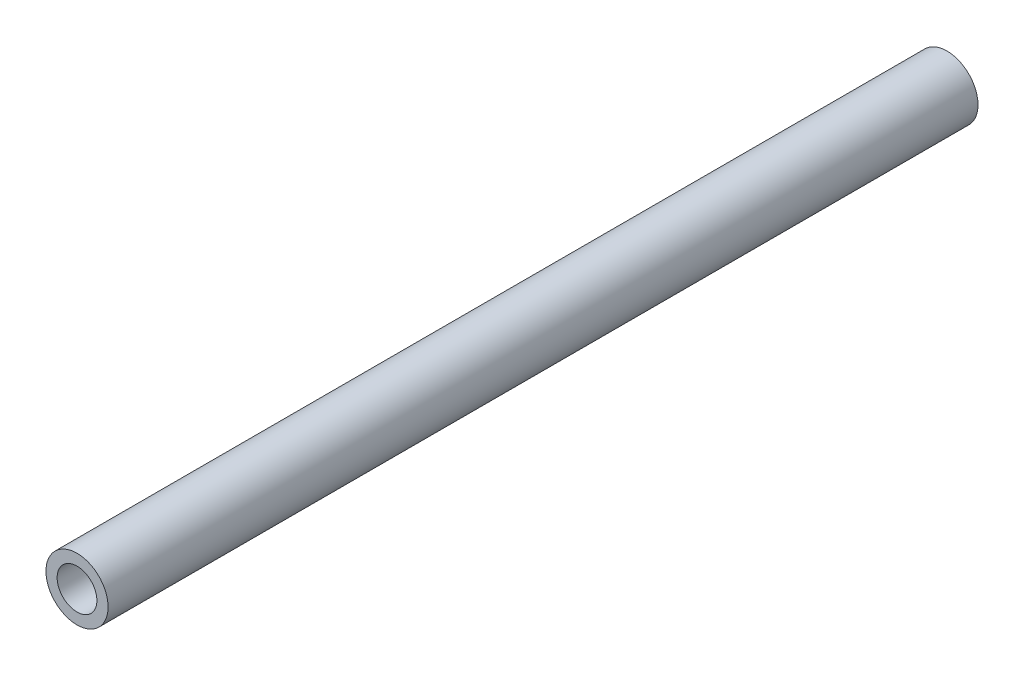
SolidWorks part; units mm, degrees
ref_plane "Front" through (0, 0, 0) normal (0, 0, 1) x (1, 0, 0)
ref_plane "Top" through (0, 0, 0) normal (0, 1, 0) x (1, 0, 0)
ref_plane "Right" through (0, 0, 0) normal (1, 0, 0) x (0, 0, -1)
sketch "Sketch1" plane through (0, 0, 0) normal (0, 0, 1) x (1, 0, 0)
  circle A0 centre (0, 0) radius 2.5
  circle A1 centre (0, 0) radius 1.6
extrude "Boss-Extrude1" add sketch "Sketch1" along normal blind 70
